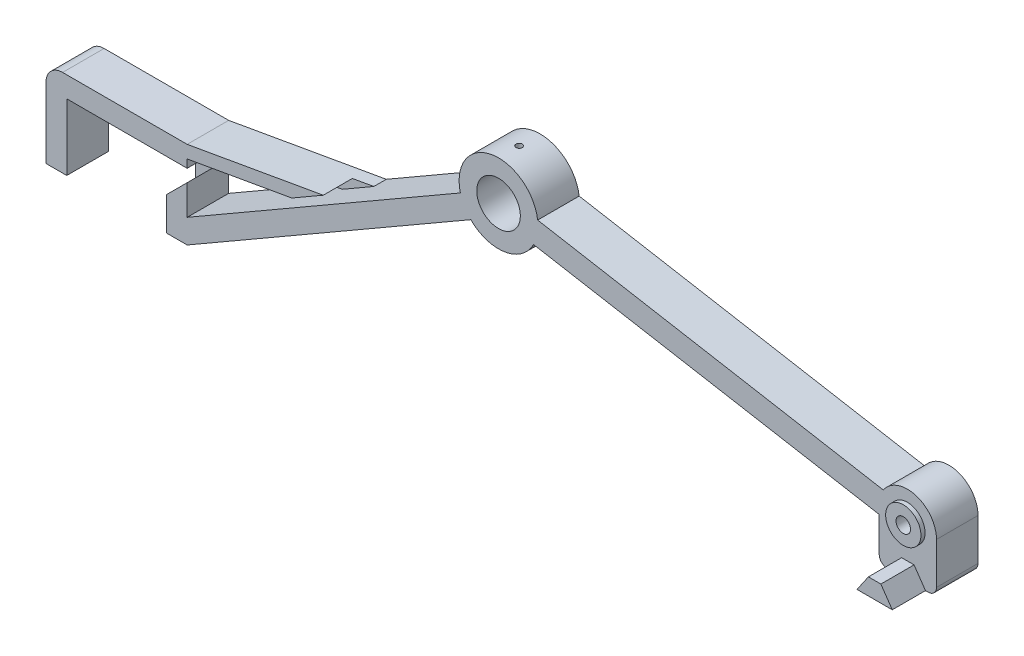
SolidWorks part; units mm, degrees
material "ABS"
ref_plane "Přední rovina" through (0, 0, 0) normal (0, 0, 1) x (1, 0, 0)
ref_plane "Horní rovina" through (0, 0, 0) normal (0, 1, 0) x (1, 0, 0)
ref_plane "Pravá rovina" through (0, 0, 0) normal (1, 0, 0) x (0, 0, -1)
sketch "Skica1" plane through (0, 0, 0) normal (0, 0, 1) x (1, 0, 0)
  line L0 (0, 0) -> (0, 16)
  line L1 (0, 16) -> (24, 16)
  line L2 (24, 16) -> (24, 0)
  line L3 (24, 0) -> (29, 0)
  line L4 (29, 0) -> (97.3127, 39.4404)
  line L5 (0, 0) -> (-5, 0)
  line L6 (-5, 0) -> (-5, 21)
  line L7 (-5, 21) -> (29, 21)
  line L8 (29, 21) -> (29, 5.7735)
  line L9 (29, 5.7735) -> (94.8127, 43.7705)
  line L10 (104, 49.0748) -> (104, 43.3013) construction
  line L11 (113.4206, 47.4137) -> (196.6749, 32.7337)
  line L12 (104, 46.188) -> (202.4808, 28.8232) construction
  line L13 (195.6876, 27.1343) -> (112.4333, 41.8143)
  line L14 (94.8127, 43.7705) -> (104, 49.0748) construction
  line L15 (104, 49.0748) -> (104, 43.3013) construction
  line L16 (104, 43.3013) -> (97.3127, 39.4404) construction
  line L18 (112.4333, 41.8143) -> (104, 43.3013) construction
  line L20 (113.4206, 47.4137) -> (104, 49.0748) construction
  arc A0 (97.3127, 39.4404) -> (112.4333, 41.8143) centre (104, 46.188) ccw
  arc A1 (113.4206, 47.4137) -> (94.8127, 43.7705) centre (104, 46.188) ccw
  circle A2 centre (104, 46.188) radius 5.25
  arc A3 (195.6876, 27.1343) -> (196.6749, 32.7337) centre (202.4808, 28.8232) ccw
  dimension "D11" = 19
  dimension "D12" = 10.5
  dimension "D14" = 7
  dimension "D1" = 5
  dimension "D2" = 5
  dimension "D3" = 24
  dimension "D4" = 16
  dimension "D5" = 5
  dimension "D6" = 5
  dimension "D7" = 5
  dimension "D8" = 80
  dimension "D9" = 60
  dimension "D10" = 140
  dimension "D13" = 100
extrude "Přidat vysunutím1" add sketch "Skica1" along normal mid plane 10
fillet "Zaoblit1" radius 4 1 edges at (-5, 21, 0)
sketch "Skica2" plane through (0, 0, 5) normal (0, 0, 1) x (1, 0, 0)
  circle A0 centre (202.4808, 28.8232) radius 1.75
  dimension "D1" = 3.5
sketch "Skica4" plane through (0, 0, 0) normal (0, 0, 1) x (1, 0, 0)
  line L0 (29, 21) -> (66.9691, 27.695)
  line L1 (94.8127, 43.7705) -> (29, 5.7735) construction
  line L2 (66.9691, 27.695) -> (59.3728, 23.3093)
  line L3 (59.3728, 23.3093) -> (29, 17.9537)
  line L4 (29, 5.7735) -> (29, 21) construction
  line L5 (29, 17.9537) -> (29, 21)
  dimension "D1" = 3
  dimension "D2" = 80
extrude "Přidat vysunutím3" add sketch "Skica4" along normal mid plane 10
sketch "Skica5" plane through (0, 0, 5) normal (0, 0, 1) x (1, 0, 0)
  circle A0 centre (202.4808, 28.8232) radius 1.75
  circle A1 centre (202.4808, 28.8232) radius 4.25
  dimension "D1" = 2.5
  dimension "D2" = 3.5
extrude "Přidat vysunutím4" add sketch "Skica5" along normal blind 1
sketch "Skica8" plane through (0, 0, 0) normal (0, -1, 0) x (1, 0, 0)
  line L0 (-1.5, 0) -> (25.5, 0) construction
  line L1 (12, 5) -> (12, -6.4114) construction
  line L2 (0, 5) -> (24, 5) construction
  circle A0 centre (-1.5, 0) radius 1.05
  circle A1 centre (25.5, 0) radius 1.05
  dimension "D3" = 2.1
  dimension "D1" = 27
  dimension "D2" = 13.5
extrude "Odebrat vysunutím3" cut sketch "Skica8" against normal blind 6
sketch "Skica9" plane through (0, 0, 5) normal (0, 0, 1) x (1, 0, 0)
  line L0 (24, 16) -> (29, 16)
  line L1 (29, 5.7735) -> (29, 17.9537) construction
  line L2 (29, 16) -> (29, 13)
  line L3 (29, 13) -> (24, 8)
  line L4 (24, 16) -> (24, 0) construction
  line L5 (24, 8) -> (24, 16)
  dimension "D1" = 45
  dimension "D2" = 3
extrude "Odebrat vysunutím4" cut sketch "Skica9" against normal blind 7
extrude "Odebrat vysunutím5" cut sketch "Skica2" against normal blind 10
sketch "Skica10" plane through (0, 0, -5) normal (0, 0, -1) x (-1, 0, 0)
  circle A0 centre (-202.4808, 28.8232) radius 3.5
  dimension "D1" = 7
extrude "Odebrat vysunutím6" cut sketch "Skica10" against normal blind 3
sketch "Skica11" plane through (0, 0, 0) normal (0, 1, 0) x (1, 0, 0)
  line L0 (103.9603, 0) -> (94.5, 0) construction
  line L1 (94.5, 5) -> (94.5, -5) construction
  line L3 (113.4206, 5) -> (94.5, 5) construction
  line L4 (103.9603, 5) -> (103.9603, 0) construction
  circle A0 centre (103.9603, 0) radius 0.75
  dimension "D1" = 1.5
extrude "Odebrat vysunutím7" cut sketch "Skica11" along normal blind 10 from offset 50
sketch "Skica12" plane through (0, 0, 5) normal (0, 0, 1) x (1, 0, 0)
  line L1 (195.6876, 27.1343) -> (195.6876, 16.8232)
  line L2 (209.4808, 28.8232) -> (209.4808, 16.8232)
  line L3 (195.6876, 16.8232) -> (209.4808, 16.8232)
  arc A0 (195.6876, 27.1343) -> (196.6749, 32.7337) centre (202.4808, 28.8232) ccw construction
  arc A1 (195.6876, 27.1343) -> (209.4808, 28.8232) centre (202.4808, 28.8232) ccw
  dimension "D1" = 12
extrude "Přidat vysunutím5" add sketch "Skica12" against normal up to surface (10 mm away) up to face at (198.9808, 28.8232, -5)
sketch "Skica13" plane through (0, 0, 5) normal (0, 0, 1) x (1, 0, 0)
  line L0 (195.6876, 16.8232) -> (209.4808, 16.8232) construction
  line L1 (201.0842, 20.8232) -> (204.0842, 20.8232)
  line L2 (201.0842, 20.8232) -> (198.3342, 16.8232)
  line L3 (198.3342, 16.8232) -> (206.8342, 16.8232)
  line L4 (204.0842, 20.8232) -> (206.8342, 16.8232)
  line L5 (201.0842, 20.8232) -> (206.8342, 16.8232) construction
  line L6 (198.3342, 16.8232) -> (204.0842, 20.8232) construction
  line L7 (202.5842, 19.7797) -> (202.5842, 16.8232) construction
  point P0 (202.5842, 19.7797)
  dimension "D1" = 3
  dimension "D2" = 4
  dimension "D3" = 8.5
extrude "Přidat vysunutím6" add sketch "Skica13" along normal blind 8
fillet "Zaoblit2" radius 2 2 edges at (209.4808, 16.8232, 0) (195.6876, 16.8232, 0)
sketch "Skica14" plane through (0, 0, 5) normal (0, 0, 1) x (1, 0, 0)
  line L0 (59.3728, 23.3093) -> (66.9691, 27.695)
  line L1 (66.9691, 27.695) -> (61.7862, 26.7811)
  line L2 (66.9691, 27.695) -> (29, 21) construction
  line L3 (61.7862, 26.7811) -> (54.1899, 22.3954)
  line L4 (29, 17.9537) -> (59.3728, 23.3093) construction
  line L5 (54.1899, 22.3954) -> (59.3728, 23.3093)
  dimension "D1" = 1.8
extrude "Odebrat vysunutím8" cut sketch "Skica14" against normal up to surface (7 mm away) up to face at (26.5, 13.25, -2)
equation "\"D2@Skica8\"=\"D1@Skica8\"/2"
